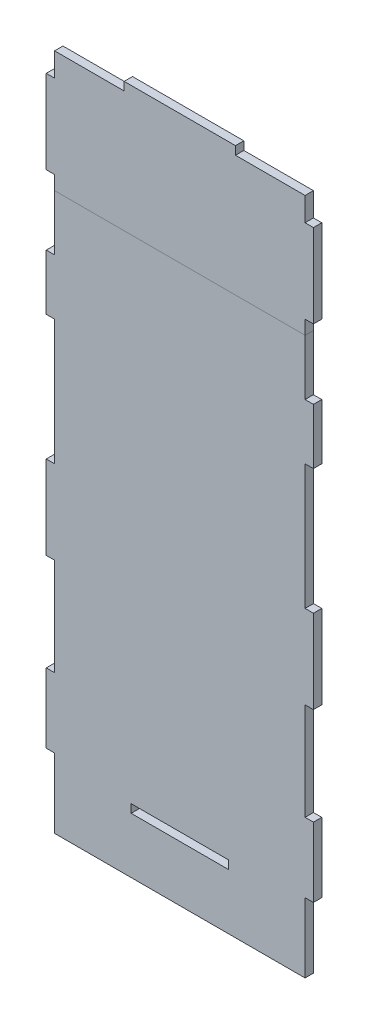
SolidWorks part; units mm, degrees
ref_plane "Front" through (0, 0, 0) normal (0, 0, 1) x (1, 0, 0)
ref_plane "Top" through (0, 0, 0) normal (0, 1, 0) x (1, 0, 0)
ref_plane "Right" through (0, 0, 0) normal (1, 0, 0) x (0, 0, -1)
sketch "Sketch1" plane through (0, 0, 0) normal (0, 0, 1) x (1, 0, 0)
  line L1 (0, 0) -> (90, 0)
  line L2 (0, 0) -> (0, 200)
  line L3 (0, 200) -> (90, 200)
  line L4 (90, 0) -> (90, 200)
  dimension "D1" = 90
  dimension "D2" = 200
extrude "Boss-Extrude1" add sketch "Sketch1" along normal blind 3
sketch "Sketch2" plane through (0, 0, 3) normal (0, 0, 1) x (1, 0, 0)
  line L0 (0, 180) -> (-23, 180)
  line L1 (0, 180) -> (0, 160)
  line L2 (0, 200) -> (0, 0) construction
  line L3 (90, 200) -> (0, 200) construction
  line L4 (-23, 180) -> (-23, 160)
  line L5 (-23, 160) -> (0, 160)
  line L6 (0, 0) -> (90, 0) construction
  line L7 (0, 115) -> (-23, 115)
  line L8 (-23, 115) -> (-23, 85)
  line L9 (-23, 85) -> (0, 85)
  line L10 (0, 40) -> (-23, 40)
  line L11 (-23, 40) -> (-23, 20)
  line L12 (-23, 20) -> (0, 20)
  line L13 (90, 180) -> (113, 180)
  line L14 (90, 0) -> (90, 200) construction
  line L15 (0, 115) -> (0, 85)
  line L16 (113, 180) -> (113, 160)
  line L17 (113, 160) -> (90, 160)
  line L18 (90, 115) -> (113, 115)
  line L19 (113, 115) -> (113, 85)
  line L20 (113, 85) -> (90, 85)
  line L21 (90, 40) -> (113, 40)
  line L22 (113, 40) -> (113, 20)
  line L23 (113, 20) -> (90, 20)
  line L24 (0, 40) -> (0, 20)
  line L25 (90, 40) -> (90, 20)
  line L26 (90, 85) -> (90, 115)
  line L27 (90, 180) -> (90, 160)
  circle A0 centre (-11.5, 170) radius 2.5
  circle A1 centre (101.5, 170) radius 2.5
  circle A2 centre (101.5, 100) radius 2.5
  circle A3 centre (-11.5, 100) radius 2.5
  circle A4 centre (-11.5, 30) radius 2.5
  circle A5 centre (101.5, 30) radius 2.5
  point P40 (-23, 170)
  point P41 (-23, 100)
  point P42 (0, 100)
  point P43 (-23, 30)
  point P44 (-11.5, 180)
  point P45 (101.5, 180)
  line M21 (0, 200) -> (0, 0)
  line M23 (90, 0) -> (90, 200)
  dimension "D3" = 20
  dimension "D4" = 30
  dimension "D6" = 5
  dimension "D7" = 5
  dimension "D8" = 5
  dimension "D9" = 5
  dimension "D10" = 5
  dimension "D11" = 5
  dimension "D1" = 23
  dimension "D2" = 23
  dimension "D5" = 20
  dimension "D12" = 20
  dimension "D13" = 20
sketch "Sketch3" plane through (0, 0, 3) normal (0, 0, 1) x (1, 0, 0)
  line L0 (0, 200) -> (0, 0) construction
  line L1 (-3, 180) -> (0, 180)
  line L2 (-3, 180) -> (-3, 160)
  line L3 (-3, 160) -> (0, 160)
  line L4 (0, 180) -> (0, 160)
  line L5 (90, 180) -> (93, 180)
  line L6 (90, 180) -> (90, 160)
  line L7 (90, 160) -> (93, 160)
  line L8 (93, 180) -> (93, 160)
  line L9 (90, 115) -> (93, 115)
  line L10 (90, 115) -> (90, 85)
  line L11 (90, 85) -> (93, 85)
  line L12 (93, 115) -> (93, 85)
  line L13 (0, 115) -> (-3, 115)
  line L14 (0, 115) -> (0, 85)
  line L15 (0, 85) -> (-3, 85)
  line L16 (-3, 115) -> (-3, 85)
  line L17 (-3, 50) -> (0, 50)
  line L18 (-3, 50) -> (-3, 25)
  line L19 (-3, 25) -> (0, 25)
  line L20 (0, 50) -> (0, 25)
  line L21 (90, 50) -> (93, 50)
  line L22 (90, 50) -> (90, 25)
  line L23 (90, 25) -> (93, 25)
  line L24 (93, 50) -> (93, 25)
  line L25 (90, 0) -> (90, 200) construction
  line L26 (0, 100) -> (90, 100) construction
  line L27 (90, 200) -> (0, 200) construction
  line L28 (0, 0) -> (90, 0) construction
  point P30 (0, 100)
  dimension "D1" = 3
  dimension "D2" = 3
  dimension "D3" = 20
  dimension "D4" = 30
  dimension "D5" = 25
  dimension "D6" = 20
  dimension "D7" = 25
extrude "Boss-Extrude2" add sketch "Sketch3" against normal blind 3
extrude "Boss-Extrude3" [suppressed] add sketch "Sketch2" against normal blind 3 contours L4 L5 L0 A0 M21 | L17 L16 L13 A1 M23 | L20 L19 L18 A2 M23 | L8 L9 L7 A3 M21 | L11 L12 L10 A4 M21 | L23 L22 L21 A5 M23
sketch "Sketch4" plane through (0, 0, 3) normal (0, 0, 1) x (1, 0, 0)
  line L1 (0, 200) -> (90, 200)
  line L2 (0, 200) -> (0, 243.5)
  line L3 (0, 243.5) -> (90, 243.5)
  line L4 (90, 200) -> (90, 243.5)
  line L5 (25, 243.5) -> (65, 243.5)
  line L6 (25, 243.5) -> (25, 246.5)
  line L7 (25, 246.5) -> (65, 246.5)
  line L8 (65, 243.5) -> (65, 246.5)
  point P10 (45, 243.5)
  line M33 (90, 200) -> (0, 200)
  dimension "D1" = 43.5
  dimension "D2" = 3
  dimension "D3" = 40
extrude "Boss-Extrude4" add sketch "Sketch4" against normal blind 3 separate body contours L4 L3 L2 M33 | L3 L8 L7 L6
sketch "Sketch5" [suppressed] plane through (0, 0, 3) normal (0, 0, 1) x (1, 0, 0)
  line L1 (0, 0) -> (90, 0)
  line L2 (0, 0) -> (0, 20)
  line L3 (0, 20) -> (90, 20)
  line L4 (90, 0) -> (90, 20)
extrude "Cut-Extrude1" [suppressed] cut sketch "Sketch5" against normal blind 10
sketch "Sketch6" [suppressed] plane through (0, 0, 0) normal (0, 0, -1) x (-1, 0, 0)
  line L0 (-113, 180) -> (-90, 180) construction
  line L1 (-113, 180) -> (-93, 180)
  line L2 (-113, 180) -> (-113, 20)
  line L3 (-113, 20) -> (-93, 20)
  line L4 (-93, 180) -> (-93, 20)
  line L5 (23, 180) -> (3, 180)
  line L6 (23, 180) -> (23, 20)
  line L7 (23, 20) -> (3, 20)
  line L8 (3, 180) -> (3, 20)
  line L9 (23, 20) -> (0, 20) construction
  line L13 (-90, 180) -> (-90, 200) construction
  line L14 (0, 200) -> (0, 180) construction
  line L15 (-113, 180) -> (-113, 160) construction
  line L16 (23, 180) -> (23, 160) construction
  dimension "D1" = 3
  dimension "D2" = 3
extrude "Cut-Extrude2" [suppressed] cut sketch "Sketch6" against normal blind 10
sketch "Sketch7" plane through (0, 0, 0) normal (0, 0, -1) x (-1, 0, 0)
  line L1 (-62.5, 23) -> (-27.5, 23)
  line L2 (-62.5, 23) -> (-62.5, 20)
  line L3 (-62.5, 20) -> (-27.5, 20)
  line L4 (-27.5, 23) -> (-27.5, 20)
  line L5 (0, 0) -> (-90, 0) construction
  point P4 (-45, 20)
  point P5 (-45, 0)
  dimension "D1" = 3
  dimension "D2" = 35
  dimension "D3" = 20
extrude "Cut-Extrude3" cut sketch "Sketch7" against normal blind 4
sketch "Sketch8" [suppressed] plane through (0, 0, 0) normal (0, 0, -1) x (-1, 0, 0)
  line L0 (0, 0) -> (-90, 0) construction
  line L1 (-93, 169) -> (-90, 169)
  line L2 (-93, 169) -> (-93, 139)
  line L3 (-93, 139) -> (-90, 139)
  line L4 (-90, 169) -> (-90, 139)
  line L5 (-93, 109) -> (-90, 109)
  line L6 (-93, 109) -> (-93, 79)
  line L7 (-93, 79) -> (-90, 79)
  line L8 (-90, 109) -> (-90, 79)
  line L9 (-93, 49) -> (-90, 49)
  line L10 (-93, 49) -> (-93, 19)
  line L11 (-93, 19) -> (-90, 19)
  line L12 (-90, 49) -> (-90, 19)
  line L13 (0, 169) -> (3, 169)
  line L14 (0, 169) -> (0, 139)
  line L15 (0, 139) -> (3, 139)
  line L16 (3, 169) -> (3, 139)
  line L17 (0, 109) -> (3, 109)
  line L18 (0, 109) -> (0, 79)
  line L19 (0, 79) -> (3, 79)
  line L20 (3, 109) -> (3, 79)
  line L21 (0, 49) -> (3, 49)
  line L22 (0, 49) -> (0, 19)
  line L23 (0, 19) -> (3, 19)
  line L24 (3, 49) -> (3, 19)
  line L25 (-90, 0) -> (-90, 200) construction
  line L26 (0, 200) -> (0, 0) construction
  dimension "D1" = 3
  dimension "D2" = 3
  dimension "D4" = 30
  dimension "D3" = 19
  dimension "D5" = 30
  dimension "D6" = 30
  dimension "D7" = 30
  dimension "D8" = 30
extrude "Boss-Extrude5" [suppressed] add sketch "Sketch8" against normal blind 3
sketch "Sketch9" [suppressed] plane through (0, 0, 0) normal (0, 0, -1) x (-1, 0, 0)
  line L0 (-90, 169) -> (-93, 169) construction
  line L1 (-90, 200) -> (0, 200)
  line L2 (-90, 200) -> (-90, 172)
  line L3 (-90, 172) -> (0, 172)
  line L4 (0, 200) -> (0, 172)
  dimension "D1" = 3
extrude "Cut-Extrude4" [suppressed] cut sketch "Sketch9" against normal blind 4
sketch "Sketch10" [suppressed] plane through (0, 0, 3) normal (0, 0, 1) x (1, 0, 0)
  line L0 (10, 172) -> (30, 172)
  line L1 (30, 172) -> (27.5, 12)
  line L2 (27.5, 12) -> (12.5, 12)
  line L3 (12.5, 12) -> (10, 172)
  line L4 (90, 172) -> (0, 172) construction
  line L5 (0, 0) -> (90, 0) construction
  line L6 (20, 172) -> (20, 12) construction
  line L7 (60, 172) -> (62.5, 12)
  line L8 (62.5, 12) -> (77.5, 12)
  line L9 (77.5, 12) -> (80, 172)
  line L10 (80, 172) -> (60, 172)
  line L11 (70, 172) -> (70, 12) construction
  line L12 (20, 172) -> (70, 172) construction
  point P8 (20, 172)
  point P9 (20, 12)
  point P12 (45, 172)
  point P15 (70, 172)
  point P18 (70, 12)
  point P21 (45, 172)
  dimension "D3" = 20
  dimension "D6" = 20
  dimension "D1" = 12
  dimension "D2" = 15
  dimension "D7" = 15
  dimension "D4" = 50
extrude "Cut-Extrude5" [suppressed] cut sketch "Sketch10" against normal through all
fillet "Fillet1" [suppressed] radius 3
sketch "Sketch11" [suppressed] plane through (0, 0, 3) normal (0, 0, 1) x (1, 0, 0)
  line L1 (0, 0) -> (90, 0)
  line L2 (0, 0) -> (0, -1)
  line L3 (0, -1) -> (90, -1)
  line L4 (90, 0) -> (90, -1)
  dimension "D1" = 1
extrude "Boss-Extrude6" [suppressed] add sketch "Sketch11" against normal blind 3
sketch "Sketch12" plane through (0, 0, 3) normal (0, 0, 1) x (1, 0, 0)
  line L0 (0, 200) -> (0, 243.5) construction
  line L1 (-3, 235) -> (0, 235)
  line L2 (-3, 235) -> (-3, 205)
  line L3 (-3, 205) -> (0, 205)
  line L4 (0, 235) -> (0, 205)
  line L5 (90, 235) -> (93, 235)
  line L6 (90, 235) -> (90, 205)
  line L7 (90, 205) -> (93, 205)
  line L8 (93, 235) -> (93, 205)
  line L9 (90, 200) -> (90, 243.5) construction
  line L10 (90, 200) -> (0, 200) construction
  dimension "D2" = 3
  dimension "D1" = 30
  dimension "D3" = 3
  dimension "D4" = 5
extrude "Boss-Extrude7" add sketch "Sketch12" against normal blind 3
equation "\"D2@Sketch3\"=\"D1@Sketch3\""
equation "\"D2@Sketch2\"=\"D1@Sketch2\""
equation "\"D7@Sketch2\"=\"D6@Sketch2\""
equation "\"D8@Sketch2\"=\"D6@Sketch2\""
equation "\"D11@Sketch2\"=\"D6@Sketch2\""
equation "\"D10@Sketch2\"=\"D6@Sketch2\""
equation "\"D9@Sketch2\"=\"D6@Sketch2\""
equation "\"D5@Sketch2\"=\"D3@Sketch2\""
equation "\"D13@Sketch2\"=\"D12@Sketch2\""
equation "\"D2@Sketch6\"=\"D1@Sketch6\""
equation "\"D2@Sketch8\"=\"D1@Sketch8\""
equation "\"D6@Sketch8\"=\"D5@Sketch8\""
equation "\"D4@Sketch8\"=\"D5@Sketch8\""
equation "\"D7@Sketch8\"=\"D8@Sketch8\""
equation "\"D6@Sketch10\"=\"D3@Sketch10\""
equation "\"D7@Sketch10\"=\"D2@Sketch10\""
equation "\"D3@Sketch12\"=\"D2@Sketch12\""
